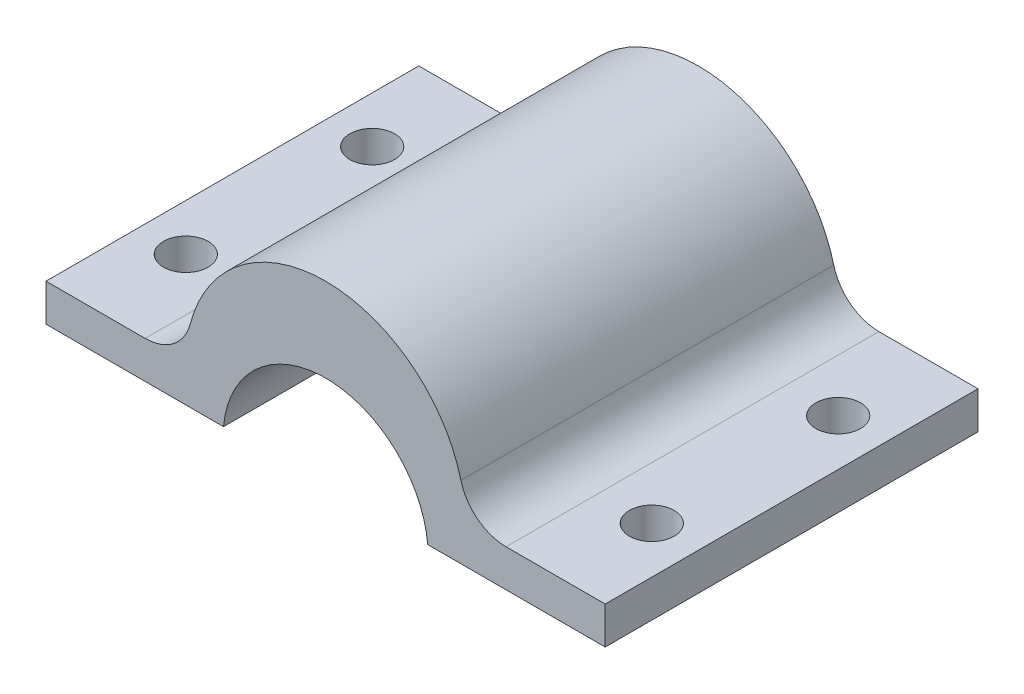
SolidWorks part; units mm, degrees
ref_plane "Plan de face" through (0, 0, 0) normal (0, 0, 1) x (1, 0, 0)
ref_plane "Plan de dessus" through (0, 0, 0) normal (0, 1, 0) x (1, 0, 0)
ref_plane "Plan de droite" through (0, 0, 0) normal (1, 0, 0) x (0, 0, -1)
sketch "Esquisse1" plane through (0, 0, 0) normal (0, 0, 1) x (1, 0, 0)
  line L0 (0, 0) -> (60, 0) construction
  line L1 (60, 0) -> (60, 5)
  line L2 (0, 0) -> (0, 5)
  line L3 (0, 5) -> (60, 5) construction
  line L4 (0, 5) -> (15, 5)
  line L9 (45, 5) -> (60, 5)
  line L10 (60, 0) -> (41, 0)
  line L11 (19, 0) -> (0, 0)
  arc A0 (45, 5) -> (15, 5) centre (30, 5) ccw
  arc A1 (19, 0) -> (41, 0) centre (30, 0) cw
  point P8 (30, 0)
  dimension "D1" = 60
  dimension "D2" = 5
extrude "mors_amovible" add sketch "Esquisse1" along normal blind 40
sketch "Esquisse2" plane through (0, 5, 0) normal (0, 1, 0) x (1, 0, 0)
  line L0 (15, 0) -> (0, 0) construction
  line L1 (0, -40) -> (0, 0) construction
  line L2 (60, 0) -> (45, 0) construction
  line L3 (60, -40) -> (60, 0) construction
  line L4 (60, -40) -> (45, -40) construction
  line L5 (15, -40) -> (0, -40) construction
  circle A0 centre (5, -10) radius 2.4
  circle A1 centre (55, -10) radius 2.4
  circle A2 centre (55, -30) radius 2.4
  circle A3 centre (5, -30) radius 2.4
  dimension "D1" = 10
  dimension "D5" = 5
  dimension "D2" = 5
  dimension "D3" = 10
  dimension "D4" = 5
  dimension "D6" = 5
  dimension "D7" = 10
  dimension "D8" = 10
extrude "trou_fixation" cut sketch "Esquisse2" against normal through all
fillet "Congé1" radius 5 2 edges at (15, 5, 20) (45, 5, 20)
sketch "Esquisse3" plane through (0, 0, 0) normal (0, 0, -1) x (-1, 0, 0)
  line L0 (0, 5) -> (0, 0) construction
  line L1 (-60, 0) -> (0, 0)
  line L2 (-60, 0) -> (-60, 1)
  line L3 (-60, 1) -> (0, 1)
  line L4 (0, 0) -> (0, 1)
  dimension "D1" = 1
extrude "Enlèv. mat.-Extru.1" cut sketch "Esquisse3" against normal up to next
